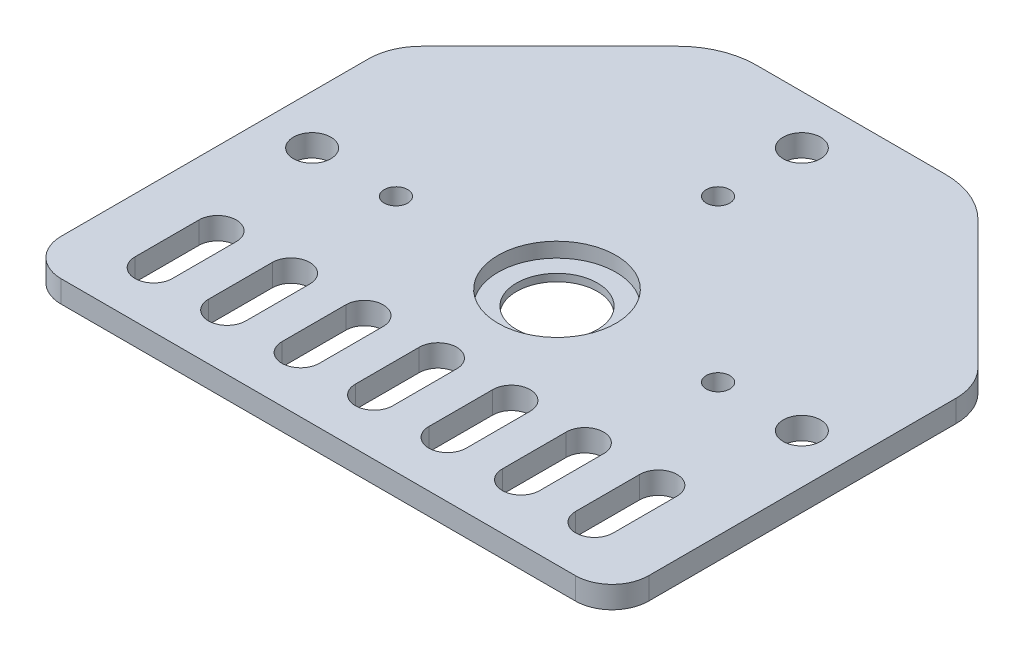
SolidWorks part; units mm, degrees
material "6061-T6 (SS)"
ref_plane "Front Plane" through (0, 0, 0) normal (0, 0, 1) x (1, 0, 0)
ref_plane "Top Plane" through (0, 0, 0) normal (0, 1, 0) x (1, 0, 0)
ref_plane "Right Plane" through (0, 0, 0) normal (1, 0, 0) x (0, 0, -1)
sketch "Sketch1" plane through (0, 0, 0) normal (0, 1, 0) x (1, 0, 0)
  line L0 (0, 0) -> (21.9203, 0) construction
  line L1 (35, -32.5) -> (-35, -32.5)
  line L2 (40, -27.5) -> (40, 14.307)
  line L3 (12.8862, 40) -> (-12.8862, 40)
  line L4 (-40, -27.5) -> (-40, 14.307)
  line L5 (0, 21.9203) -> (0, 0) construction
  line L6 (-37.8765, 19.4335) -> (-20.4381, 36.8719)
  line L7 (37.8765, 19.4335) -> (20.4381, 36.8719)
  line L8 (30, -24.9) -> (30, -16.2) construction
  line L9 (27.45, -24.9) -> (27.45, -16.2)
  line L10 (32.55, -24.9) -> (32.55, -16.2)
  line L11 (20, -24.9) -> (20, -16.2) construction
  line L12 (17.45, -24.9) -> (17.45, -16.2)
  line L13 (22.55, -24.9) -> (22.55, -16.2)
  line L14 (10, -24.9) -> (10, -16.2) construction
  line L15 (7.45, -24.9) -> (7.45, -16.2)
  line L16 (12.55, -24.9) -> (12.55, -16.2)
  line L17 (0, -24.9) -> (0, -16.2) construction
  line L18 (-2.55, -24.9) -> (-2.55, -16.2)
  line L19 (2.55, -24.9) -> (2.55, -16.2)
  line L20 (-10, -24.9) -> (-10, -16.2) construction
  line L21 (-12.55, -24.9) -> (-12.55, -16.2)
  line L22 (-7.45, -24.9) -> (-7.45, -16.2)
  line L23 (30, -24.9) -> (20, -24.9) construction
  line L24 (-20, -24.9) -> (-20, -16.2) construction
  line L25 (-22.55, -24.9) -> (-22.55, -16.2)
  line L26 (-17.45, -24.9) -> (-17.45, -16.2)
  line L27 (-30, -24.9) -> (-30, -16.2) construction
  line L28 (-32.55, -24.9) -> (-32.55, -16.2)
  line L29 (-27.45, -24.9) -> (-27.45, -16.2)
  line L30 (0, 0) -> (-33.333, 0) construction
  line L31 (0, 0) -> (0, 33.333) construction
  arc A0 (-35, -32.5) -> (-40, -27.5) centre (-35, -27.5) cw
  arc A1 (35, -32.5) -> (40, -27.5) centre (35, -27.5) ccw
  circle A2 centre (21.9203, 0) radius 1.6
  circle A3 centre (-21.9203, 0) radius 1.6
  circle A4 centre (0, 0) radius 5.5
  circle A5 centre (0, 21.9203) radius 1.6
  arc A6 (27.45, -24.9) -> (32.55, -24.9) centre (30, -24.9) ccw
  arc A7 (32.55, -16.2) -> (27.45, -16.2) centre (30, -16.2) ccw
  arc A8 (17.45, -24.9) -> (22.55, -24.9) centre (20, -24.9) ccw
  arc A9 (22.55, -16.2) -> (17.45, -16.2) centre (20, -16.2) ccw
  arc A10 (7.45, -24.9) -> (12.55, -24.9) centre (10, -24.9) ccw
  arc A11 (12.55, -16.2) -> (7.45, -16.2) centre (10, -16.2) ccw
  arc A12 (-2.55, -24.9) -> (2.55, -24.9) centre (0, -24.9) ccw
  arc A13 (2.55, -16.2) -> (-2.55, -16.2) centre (0, -16.2) ccw
  arc A14 (-12.55, -24.9) -> (-7.45, -24.9) centre (-10, -24.9) ccw
  arc A15 (-7.45, -16.2) -> (-12.55, -16.2) centre (-10, -16.2) ccw
  arc A16 (-37.8765, 19.4335) -> (-40, 14.307) centre (-32.75, 14.307) ccw
  arc A17 (37.8765, 19.4335) -> (40, 14.307) centre (32.75, 14.307) cw
  arc A18 (-20.4381, 36.8719) -> (-12.8862, 40) centre (-12.8862, 29.32) cw
  arc A19 (12.8862, 40) -> (20.4381, 36.8719) centre (12.8862, 29.32) cw
  arc A20 (-22.55, -24.9) -> (-17.45, -24.9) centre (-20, -24.9) ccw
  arc A21 (-17.45, -16.2) -> (-22.55, -16.2) centre (-20, -16.2) ccw
  arc A22 (-32.55, -24.9) -> (-27.45, -24.9) centre (-30, -24.9) ccw
  arc A23 (-27.45, -16.2) -> (-32.55, -16.2) centre (-30, -16.2) ccw
  circle A24 centre (-33.333, 0) radius 2.55
  circle A25 centre (0, 33.333) radius 2.55
  circle A26 centre (33.333, 0) radius 2.55
  point P21 (30, -20.55)
  point P29 (20, -20.55)
  point P36 (10, -20.55)
  point P43 (0, -20.55)
  point P50 (-10, -20.55)
  point P58 (-40, 17.31)
  point P61 (40, 17.31)
  point P64 (-17.31, 40)
  point P67 (17.31, 40)
  point P70 (-20, -20.55)
  point P77 (-30, -20.55)
  dimension "D2" = 5
  dimension "D3" = 32.5
  dimension "D5" = 45
  dimension "D7" = 31
  dimension "D10" = 5.1
  dimension "D4" = 11
  dimension "D8" = 3.2
  dimension "D14" = 7
  dimension "D15" = 7.25
  dimension "D17" = 5.1
  dimension "D6" = 34.62
  dimension "D16" = 10.68
  dimension "D1" = 72.5
  dimension "D9" = 80
  dimension "D11" = 8.7
  dimension "D12" = 7.6
  dimension "D13" = 10
  dimension "D18" = 47.14
extrude "Boss-Extrude1" add sketch "Sketch1" along normal blind 3
sketch "Sketch2" plane through (0, 3, 0) normal (0, 1, 0) x (1, 0, 0)
  circle A0 centre (0, 0) radius 8.025
  dimension "D1" = 16.05
extrude "Cut-Extrude1" cut sketch "Sketch2" against normal blind 2
